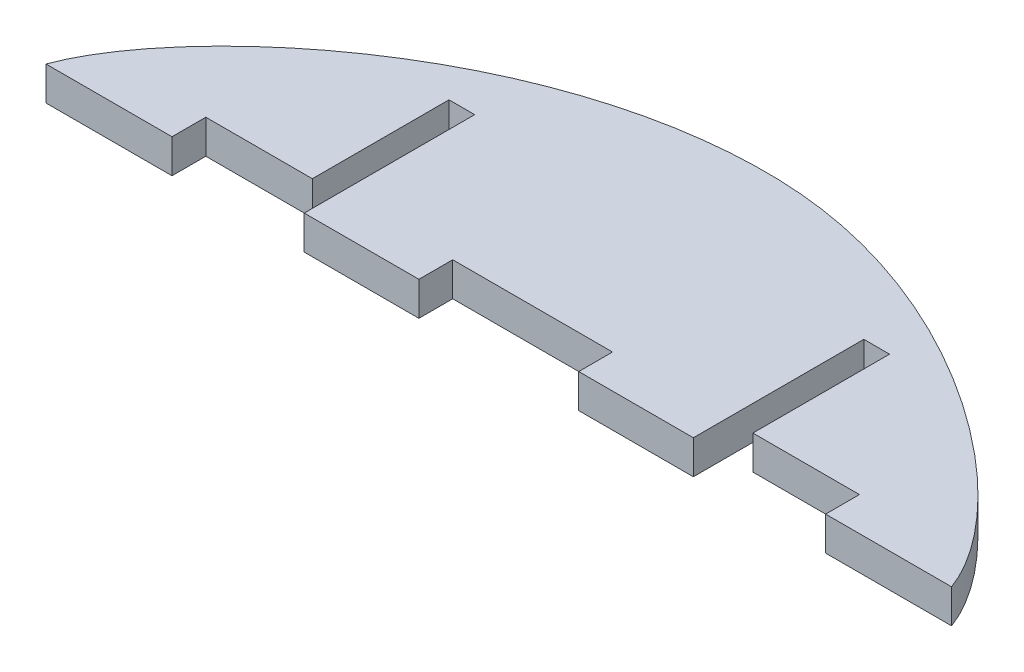
SolidWorks part; units mm, degrees
ref_plane "Front Plane" through (0, 0, 0) normal (0, 0, 1) x (1, 0, 0)
ref_plane "Top Plane" through (0, 0, 0) normal (0, 1, 0) x (1, 0, 0)
ref_plane "Right Plane" through (0, 0, 0) normal (1, 0, 0) x (0, 0, -1)
sketch "Sketch1" plane through (0, 0, 0) normal (0, 1, 0) x (1, 0, 0)
  line L0 (0, 0) -> (85, 0)
  line L1 (42.5, 0) -> (42.5, 25)
  line L2 (57.3517, 25) -> (25.0748, 25) construction
  line L3 (40.1734, 110.3755) -> (-35.3127, -97.0208) construction
  line L4 (121.6855, -100.7925) -> (37.844, 129.56) construction
  spline S0 degree 3 poles (0, 0) (3.0782, 8.4572) (20.6793, 24.7062) (61.0739, 25.5204) (81.9218, 8.4572) (85, 0) knots 0 0 0 0 0.479832 0.579832 1 1 1 1
  dimension "D3" = 120
  dimension "D4" = 70
  dimension "D5" = 70
  dimension "D6" = 30
  dimension "D7" = 30
  dimension "D1" = 85
  dimension "D2" = 25
extrude "Boss-Extrude1" add sketch "Sketch1" along normal blind 3.175 contours S0 L0 L1 | S0 L1 L0
sketch "Sketch2" plane through (0, 0, 0) normal (0, -1, 0) x (1, 0, 0)
  line L0 (0, 0) -> (85, 0) construction
  line L1 (60.762, -16) -> (63.175, -16)
  line L2 (60.762, -16) -> (60.762, 0)
  line L3 (60.762, 0) -> (63.175, 0)
  line L4 (63.175, -16) -> (63.175, 0)
  line L5 (63.175, 0) -> (63.175, -15) construction
  line L6 (21.825, 0) -> (21.825, -15) construction
  line L7 (63.175, 0) -> (73.175, 0)
  line L8 (63.175, 0) -> (63.175, -3.175)
  line L9 (63.175, -3.175) -> (73.175, -3.175)
  line L10 (73.175, 0) -> (73.175, -3.175)
  line L11 (24.238, -16) -> (21.825, -16)
  line L12 (24.238, -16) -> (24.238, 0)
  line L13 (24.238, 0) -> (21.825, 0)
  line L14 (21.825, -16) -> (21.825, 0)
  line L16 (21.825, 0) -> (11.825, 0)
  line L17 (21.825, 0) -> (21.825, -3.175)
  line L18 (21.825, -3.175) -> (11.825, -3.175)
  line L19 (11.825, 0) -> (11.825, -3.175)
  line L20 (50, 0) -> (35, 0)
  line L21 (50, 0) -> (50, -3.175)
  line L22 (50, -3.175) -> (35, -3.175)
  line L23 (35, 0) -> (35, -3.175)
  point P26 (42.5, 0)
  point P27 (42.5, 0)
  point P28 (0, 0)
  point P29 (0, 0)
  line M6 (85, 0) -> (0, 0)
  dimension "D1" = 3.175
  dimension "D2" = 10
  dimension "D3" = 15
  dimension "D4" = 16
  dimension "D5" = 16
  dimension "D6" = 2.413
  dimension "D7" = 2.413
extrude "Cut-Extrude1" cut sketch "Sketch2" against normal through all contours L10 L4 L9 M6 | L1 L4 L2 M6 | L23 L22 L21 M6 | L14 L11 L12 M6 | L19 L18 L14 M6
